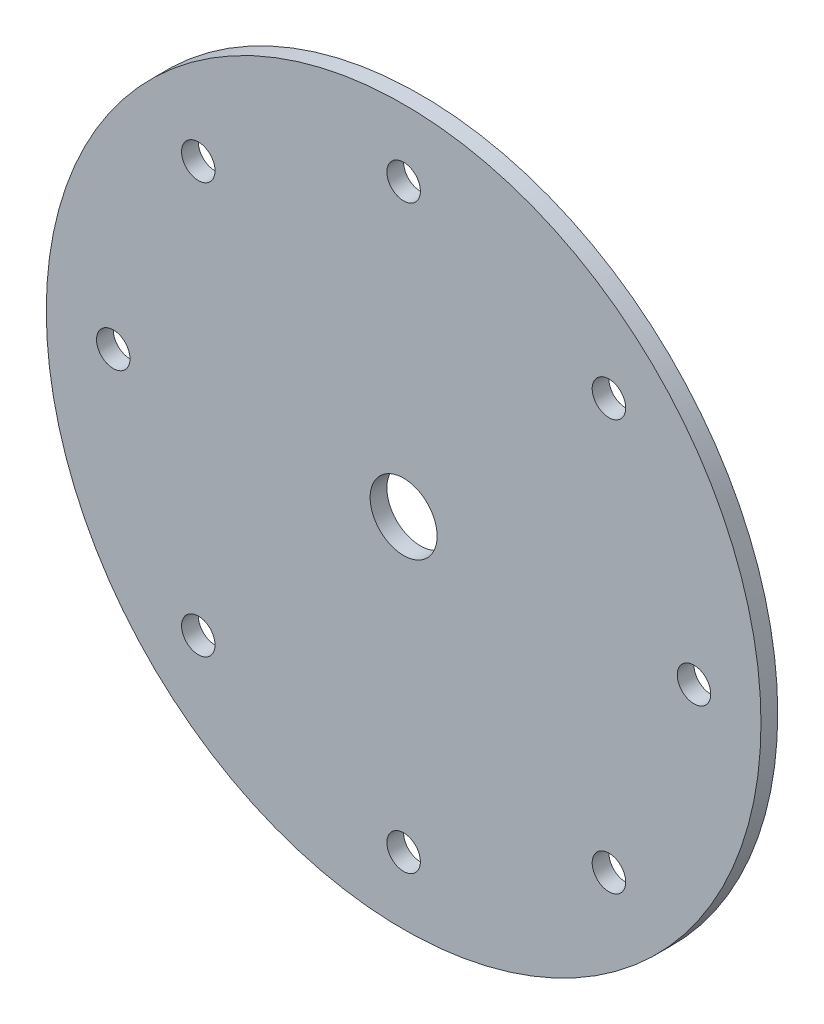
SolidWorks part; units mm, degrees
material "Plain Carbon Steel"
ref_plane "Front Plane" through (0, 0, 0) normal (0, 0, 1) x (1, 0, 0)
ref_plane "Top Plane" through (0, 0, 0) normal (0, 1, 0) x (1, 0, 0)
ref_plane "Right Plane" through (0, 0, 0) normal (1, 0, 0) x (0, 0, -1)
sketch "Sketch1" plane through (0, 0, 0) normal (0, 0, 1) x (1, 0, 0)
  line L0 (0, 101.6) -> (0, -101.6) construction
  line L1 (-101.6, 0) -> (101.6, 0) construction
  line L2 (-58.3717, 58.3717) -> (58.3717, -58.3717) construction
  line L3 (-58.3717, -58.3717) -> (58.3717, 58.3717) construction
  circle A0 centre (0, 0) radius 101.6
  circle A1 centre (0, 0) radius 9.525
  circle A2 centre (0, 82.55) radius 4.7625
  circle A6 centre (58.3717, 58.3717) radius 4.7625
  circle A7 centre (82.55, 0) radius 4.7625
  circle A8 centre (58.3717, -58.3717) radius 4.7625
  circle A9 centre (0, -82.55) radius 4.7625
  circle A10 centre (-58.3717, -58.3717) radius 4.7625
  circle A11 centre (-82.55, 0) radius 4.7625
  circle A12 centre (-58.3717, 58.3717) radius 4.7625
  dimension "D1" = 203.2
  dimension "D2" = 19.05
  dimension "D3" = 9.525
  dimension "D6" = 19.05
  dimension "D4" = 19.05
  dimension "D5" = 8
extrude "Rotor Disc" add sketch "Sketch1" along normal blind 4.7625
